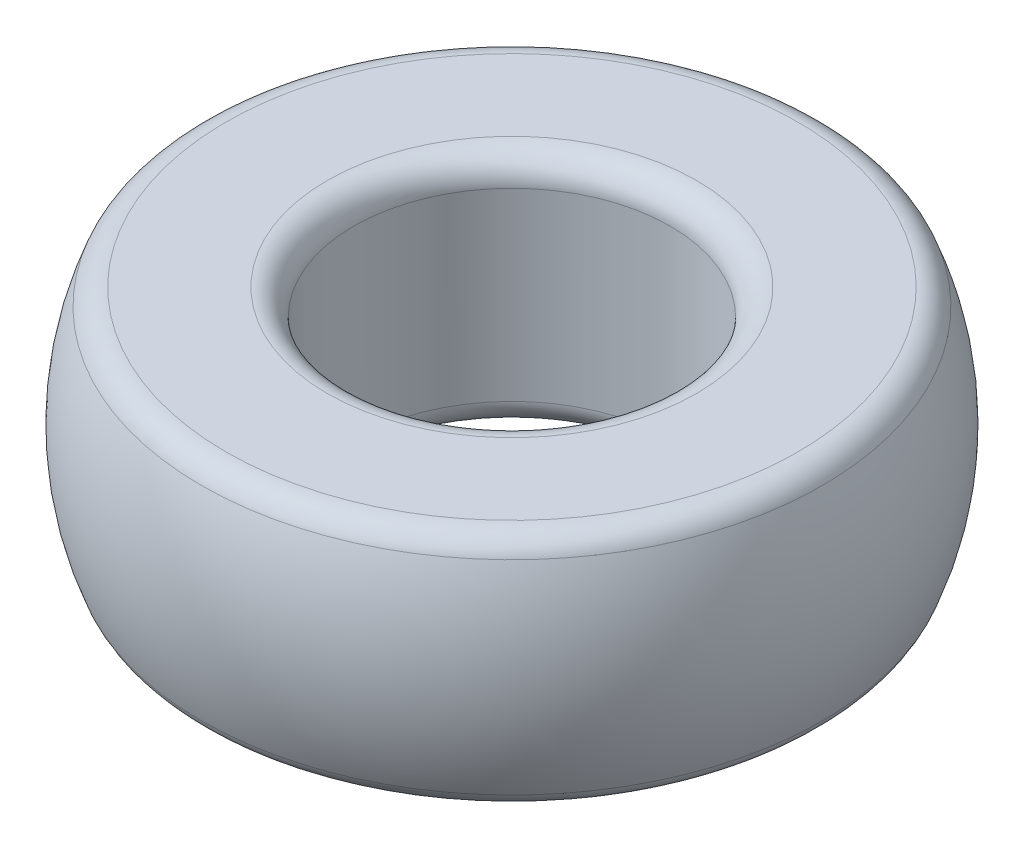
SolidWorks part; units mm, degrees
ref_plane "Front Plane" through (0, 0, 0) normal (0, 0, 1) x (1, 0, 0)
ref_plane "Top Plane" through (0, 0, 0) normal (0, 1, 0) x (1, 0, 0)
ref_plane "Right Plane" through (0, 0, 0) normal (1, 0, 0) x (0, 0, -1)
sketch "Sketch1" plane through (0, 0, 0) normal (0, 0, 1) x (1, 0, 0)
  line L0 (0, -5.9571) -> (0, 5.9571) construction
  line L1 (11.5, 4.5) -> (11.5, -4.5) construction
  line L2 (0, 0) -> (11.5, 0) construction
  line L3 (11.5, 4.5) -> (6, 4.5)
  line L4 (6, 4.5) -> (6, -4.5)
  line L5 (6, -4.5) -> (11.5, -4.5)
  line L6 (12.5, 4.3723) -> (12.5, 0) construction
  arc A0 (11.5, 4.5) -> (11.5, -4.5) centre (1.875, 0) cw
  point P4 (0, 0)
  point P8 (12.5, 0)
  point P9 (11.5, 4.5)
  point P10 (11.5, -4.5)
  dimension "D1" = 1
  dimension "Outer Diam" = 25
  dimension "Height" = 9
  dimension "Hole Diam" = 12
revolve "Revolve1" add sketch "Sketch1" angle 360 about L0
fillet "Fillet1" radius 1 4 edges at (0, -4.5, -6) (0, -4.5, -11.5) (0, 4.5, -6) (0, 4.5, -11.5)
